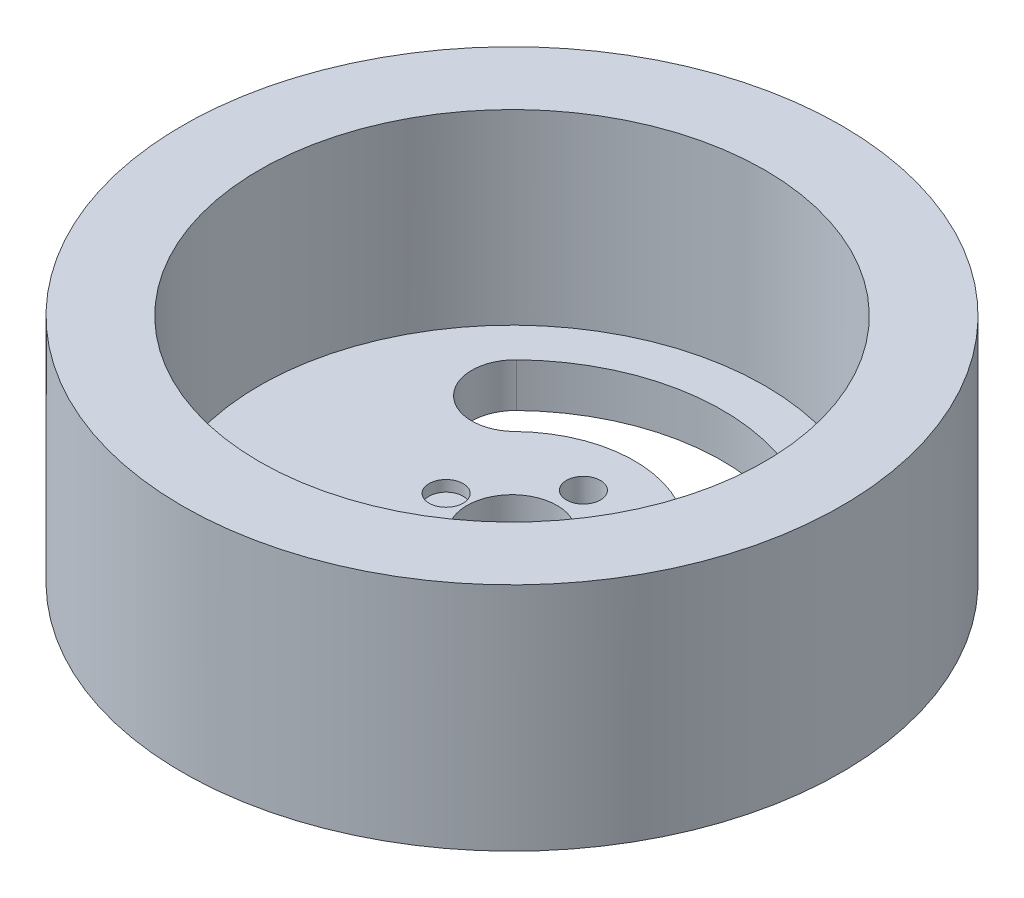
SolidWorks part; units mm, degrees
material "硅橡胶"
ref_plane "前视基准面" through (0, 0, 0) normal (0, 0, 1) x (1, 0, 0)
ref_plane "上视基准面" through (0, 0, 0) normal (0, 1, 0) x (1, 0, 0)
ref_plane "右视基准面" through (0, 0, 0) normal (1, 0, 0) x (0, 0, -1)
sketch "草图1" plane through (0, 0, 0) normal (0, 1, 0) x (1, 0, 0)
  circle A0 centre (0, 0) radius 30
  circle A1 centre (0, 0) radius 23
extrude "凸台-拉伸1" add sketch "草图1" along normal blind 21
sketch "草图2" plane through (0, 0, 0) normal (0, -1, 0) x (1, 0, 0)
  line L0 (11.55, 0) -> (-11.55, 0) construction
  circle A0 centre (0, 0) radius 23
  arc A1 (-10.5407, 10.8727) -> (10.8727, 10.5407) centre (0, 0) cw construction
  arc A2 (13.7447, 13.325) -> (-13.325, 13.7447) centre (0, 0) ccw
  arc A3 (8.0008, 7.7565) -> (-7.7565, 8.0008) centre (0, 0) ccw
  arc A4 (8.0008, 7.7565) -> (13.7447, 13.325) centre (10.8727, 10.5407) ccw
  arc A5 (-13.325, 13.7447) -> (-7.7565, 8.0008) centre (-10.5407, 10.8727) ccw
  arc A6 (-10.5407, -10.8727) -> (10.8727, -10.5407) centre (0, 0) ccw construction
  arc A7 (13.7447, -13.325) -> (-13.325, -13.7447) centre (0, 0) cw
  arc A8 (8.0008, -7.7565) -> (-7.7565, -8.0008) centre (0, 0) cw
  arc A9 (8.0008, -7.7565) -> (13.7447, -13.325) centre (10.8727, -10.5407) cw
  arc A10 (-13.325, -13.7447) -> (-7.7565, -8.0008) centre (-10.5407, -10.8727) cw
  circle A11 centre (0, 0) radius 4.1
  circle A12 centre (6, 0) radius 1.55
  circle A13 centre (-6, 0) radius 1.55
  circle A14 centre (0, 6.5) radius 1.55
  circle A15 centre (0, -6.5) radius 1.55
  point P5 (0.2348, 15.1416)
  point P14 (0.2348, -15.1416)
  dimension "D1" = 6
  dimension "D2" = 6
  dimension "D3" = 6.5
  dimension "D4" = 6.5
extrude "凸台-拉伸2" add sketch "草图2" against normal blind 1
sketch "草图3" plane through (0, 0, 0) normal (0, -1, 0) x (1, 0, 0)
  arc A0 (-7.7565, -8.0008) -> (-13.325, -13.7447) centre (-10.5407, -10.8727) ccw construction
  circle A1 centre (0, 0) radius 30
  circle A2 centre (0, 0) radius 30
  arc A3 (-13.325, -13.7447) -> (13.7447, -13.325) centre (0, 0) ccw construction
  arc A4 (13.7447, -13.325) -> (8.0008, -7.7565) centre (10.8727, -10.5407) ccw construction
  arc A5 (-7.7565, -8.0008) -> (8.0008, -7.7565) centre (0, 0) ccw construction
  circle A6 centre (0, -6.5) radius 1.55 construction
  circle A7 centre (6, 0) radius 1.55 construction
  circle A8 centre (0, 0) radius 4.1 construction
  circle A9 centre (0, 6.5) radius 1.55 construction
  arc A10 (8.0008, 7.7565) -> (13.7447, 13.325) centre (10.8727, 10.5407) ccw construction
  arc A11 (8.0008, 7.7565) -> (-7.7565, 8.0008) centre (0, 0) ccw construction
  arc A12 (13.7447, 13.325) -> (-13.325, 13.7447) centre (0, 0) ccw construction
  arc A13 (-13.325, 13.7447) -> (-7.7565, 8.0008) centre (-10.5407, 10.8727) ccw construction
  arc A14 (-7.7565, -8.0008) -> (-13.325, -13.7447) centre (-10.5407, -10.8727) ccw
  arc A15 (-13.325, -13.7447) -> (13.7447, -13.325) centre (0, 0) ccw
  arc A16 (13.7447, -13.325) -> (8.0008, -7.7565) centre (10.8727, -10.5407) ccw
  arc A17 (-7.7565, -8.0008) -> (8.0008, -7.7565) centre (0, 0) ccw
  circle A18 centre (0, -6.5) radius 1.55
  circle A19 centre (6, 0) radius 1.55
  circle A20 centre (0, 0) radius 4.1
  circle A21 centre (0, 6.5) radius 1.55
  arc A22 (8.0008, 7.7565) -> (13.7447, 13.325) centre (10.8727, 10.5407) ccw
  arc A23 (8.0008, 7.7565) -> (-7.7565, 8.0008) centre (0, 0) ccw
  arc A24 (13.7447, 13.325) -> (-13.325, 13.7447) centre (0, 0) ccw
  arc A25 (-13.325, 13.7447) -> (-7.7565, 8.0008) centre (-10.5407, 10.8727) ccw
  dimension "D1" = 0
extrude "凸台-拉伸3" add sketch "草图3" along normal blind 3
sketch "草图4" plane through (0, 21, 0) normal (0, 1, 0) x (1, 0, 0)
  circle A1 centre (0, 0) radius 30
  circle A2 centre (0, 0) radius 30
  dimension "D1" = 0
extrude "切除-拉伸1" cut sketch "草图4" against normal blind 3
